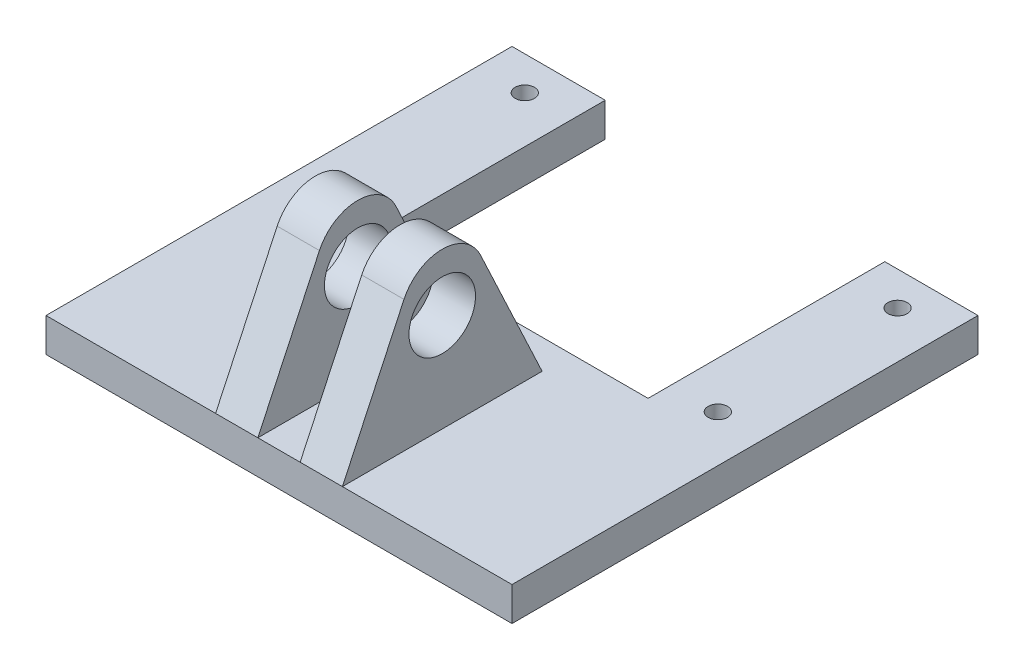
SolidWorks part; units mm, degrees
ref_plane "Front Plane" through (0, 0, 0) normal (0, 0, 1) x (1, 0, 0)
ref_plane "Top Plane" through (0, 0, 0) normal (0, 1, 0) x (1, 0, 0)
ref_plane "Right Plane" through (0, 0, 0) normal (1, 0, 0) x (0, 0, -1)
sketch "Sketch1" plane through (0, 0, 0) normal (0, 1, 0) x (1, 0, 0)
  line L0 (-17.5, 0) -> (-17.5, 35)
  line L1 (-17.5, 35) -> (-10.5, 35)
  line L2 (-10.5, 35) -> (-10.5, 17.22)
  line L3 (-10.5, 17.22) -> (10.5, 17.22)
  line L4 (10.5, 17.22) -> (10.5, 35)
  line L5 (10.5, 35) -> (17.5, 35)
  line L6 (17.5, 35) -> (17.5, 0)
  line L7 (17.5, 0) -> (-17.5, 0)
  line L8 (-14, 35) -> (-14, 0) construction
  line L9 (14, 35) -> (14, 0) construction
  circle A0 centre (-14, 32.46) radius 0.725
  circle A1 centre (-14, 18.96) radius 0.725
  circle A2 centre (14, 32.46) radius 0.725
  circle A3 centre (14, 18.96) radius 0.725
  dimension "D2" = 1.45
  dimension "D1" = 35
  dimension "D3" = 35
  dimension "D4" = 13.5
  dimension "D5" = 28
  dimension "D6" = 17.78
  dimension "D7" = 2.54
  dimension "D8" = 17.22
extrude "Boss-Extrude1" add sketch "Sketch1" along normal blind 2.54
sketch "Sketch2" plane through (0, 0, 0) normal (1, 0, 0) x (0, 0, -1)
  line L0 (15, 2.54) -> (7.5, 18.54)
  line L1 (0, 2.54) -> (35, 2.54) construction
  line L2 (7.5, 18.54) -> (0, 2.54)
  line L3 (15, 2.54) -> (0, 2.54)
  line L4 (0, 2.54) -> (-0.0326, 2.6981)
  circle A0 centre (7.5, 9.94) radius 1.651
  dimension "D1" = 3.302
  dimension "D2" = 15
  dimension "D3" = 16
  dimension "D4" = 7.4
extrude "Boss-Extrude2" add sketch "Sketch2" along normal mid plane 9.525 contours L3 L0 L2 | A0
sketch "Sketch3" plane through (0, 2.54, 0) normal (0, 1, 0) x (1, 0, 0)
  line L0 (4.7625, 0) -> (-4.7625, 0) construction
  line L1 (-1.5875, 0) -> (1.5875, 0)
  line L2 (-1.5875, 0) -> (-1.5875, 15)
  line L3 (-1.5875, 15) -> (1.5875, 15)
  line L4 (1.5875, 0) -> (1.5875, 15)
  line L5 (4.7625, 15) -> (-4.7625, 15) construction
  dimension "D1" = 3.175
extrude "Cut-Extrude1" cut sketch "Sketch3" along normal up to vertex
fillet "Fillet1" radius 3.175 2 edges at (3.175, 18.54, -7.5) (-3.175, 18.54, -7.5)
hole_wizard "Ø5.0mm Dowel Hole1" positions "Sketch4" profile "Sketch5" hole size "Ø5.0" standard "ISO"
sketch "Sketch4" plane through (-4.7625, 0, 0) normal (-1, 0, 0) x (0, 0, 1)
  point P0 (-7.5, 9.94)
sketch "Sketch5" plane through (-4.7625, 9.94, -7.5) normal (0, 1, 0) x (0, 0, 1)
  line L0 (0, 0) -> (0, 21.5022)
  line L1 (0, 21.5022) -> (2.5, 20)
  line L2 (2.5, 20) -> (2.5, 0)
  line L5 (2.5, 0) -> (0, 0)
  line L10 (0, 21.5022) -> (-2.5, 20) construction
  line L11 (0, -6.35) -> (0, 107.95) construction
  dimension "Hole Dia." = 5
  dimension "Hole Depth" = 20
  dimension "Drill Angle" = 118
